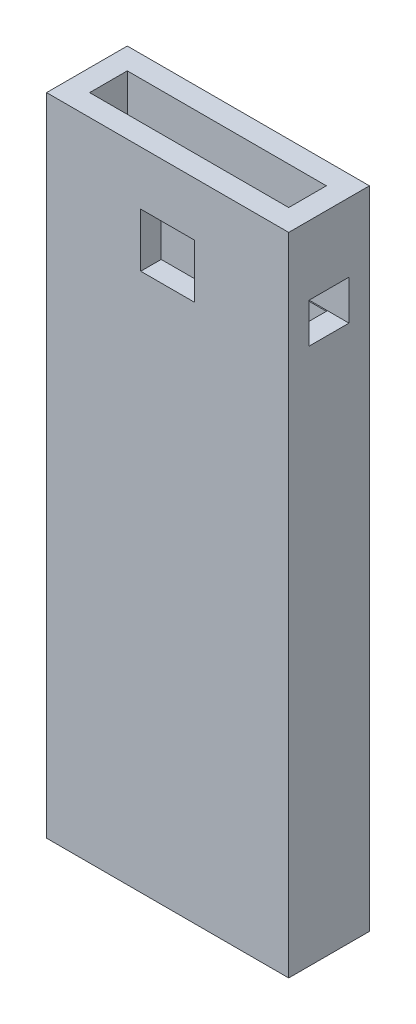
SolidWorks part; units mm, degrees
ref_plane "Front Plane" through (0, 0, 0) normal (0, 0, 1) x (1, 0, 0)
ref_plane "Top Plane" through (0, 0, 0) normal (0, 1, 0) x (1, 0, 0)
ref_plane "Right Plane" through (0, 0, 0) normal (1, 0, 0) x (0, 0, -1)
sketch "Sketch1" plane through (0, 0, 0) normal (0, 1, 0) x (1, 0, 0)
  line L1 (22.5, -7.5) -> (-22.5, -7.5)
  line L2 (22.5, -7.5) -> (22.5, 7.5)
  line L3 (22.5, 7.5) -> (-22.5, 7.5)
  line L4 (-22.5, -7.5) -> (-22.5, 7.5)
  line L5 (22.5, -7.5) -> (-22.5, 7.5) construction
  line L6 (22.5, 7.5) -> (-22.5, -7.5) construction
  point P0 (0, 0)
  dimension "D1" = 45
  dimension "D2" = 15
extrude "Boss-Extrude1" add sketch "Sketch1" along normal mid plane 120
shell "Shell1" thickness 4
sketch "Sketch3" plane through (0, -60, 0) normal (0, -1, 0) x (1, 0, 0)
  line L1 (5, -3.5) -> (-5, -3.5)
  line L2 (5, -3.5) -> (5, 3.5)
  line L3 (5, 3.5) -> (-5, 3.5)
  line L4 (-5, -3.5) -> (-5, 3.5)
  line L5 (5, -3.5) -> (-5, 3.5) construction
  line L6 (5, 3.5) -> (-5, -3.5) construction
  point P0 (0, 0)
  dimension "D1" = 10
  dimension "D2" = 7
extrude "Cut-Extrude2" cut sketch "Sketch3" against normal blind 4
sketch "Sketch4" plane through (0, 0, 7.5) normal (0, 0, 1) x (1, 0, 0)
  line L0 (0, -8.25) -> (0, 8.25) construction
  line L1 (5, 50) -> (-5, 50)
  line L2 (5, 50) -> (5, 40)
  line L3 (5, 40) -> (-5, 40)
  line L4 (-5, 50) -> (-5, 40)
  line L5 (5, 50) -> (-5, 40) construction
  line L6 (5, 40) -> (-5, 50) construction
  line L7 (-22.5, 60) -> (22.5, 60) construction
  point P0 (0, 45)
  dimension "D1" = 10
  dimension "D2" = 10
extrude "Cut-Extrude3" cut sketch "Sketch4" against normal up to next
sketch "Sketch5" plane through (22.5, 0, 0) normal (1, 0, 0) x (0, 0, -1)
  line L0 (0, 24.75) -> (0, -24.75) construction
  line L1 (3.7, 39.8) -> (-3.7, 39.8)
  line L2 (3.7, 39.8) -> (3.7, 47.2)
  line L3 (3.7, 47.2) -> (-3.7, 47.2)
  line L4 (-3.7, 39.8) -> (-3.7, 47.2)
  line L5 (3.7, 39.8) -> (-3.7, 47.2) construction
  line L6 (3.7, 47.2) -> (-3.7, 39.8) construction
  line L7 (-7.5, 60) -> (7.5, 60) construction
  point P0 (0, 43.5)
  dimension "D1" = 20.2
  dimension "D2" = 7.4
  dimension "D3" = 7.4
extrude "Cut-Extrude4" cut sketch "Sketch5" against normal through all
sketch "Sketch6" plane through (0, -60, 0) normal (0, -1, 0) x (1, 0, 0)
  line L0 (24.75, 0) -> (-24.75, 0) construction
  line L1 (-15, 4.2724) -> (-18.7, 2.1362)
  line L2 (-18.7, 2.1362) -> (-18.7, -2.1362)
  line L3 (-18.7, -2.1362) -> (-15, -4.2724)
  line L4 (-15, -4.2724) -> (-11.3, -2.1362)
  line L5 (-11.3, -2.1362) -> (-11.3, 2.1362)
  line L6 (-11.3, 2.1362) -> (-15, 4.2724)
  line L7 (0, -7.5) -> (0, 7.5) construction
  line L8 (22.5, -7.5) -> (-22.5, -7.5) construction
  line L9 (-22.5, 7.5) -> (22.5, 7.5) construction
  line L10 (11.3, 2.1362) -> (15, 4.2724)
  line L11 (11.3, -2.1362) -> (11.3, 2.1362)
  line L12 (15, -4.2724) -> (11.3, -2.1362)
  line L13 (18.7, -2.1362) -> (15, -4.2724)
  line L14 (18.7, 2.1362) -> (18.7, -2.1362)
  line L15 (15, 4.2724) -> (18.7, 2.1362)
  circle A0 centre (-15, 0) radius 3.7 construction
  circle A1 centre (15, 0) radius 3.7 construction
  dimension "D1" = 7.4
  dimension "D2" = 30
extrude "Cut-Extrude5" cut sketch "Sketch6" against normal blind 3.6 from offset 1.2 offset against normal yes
sketch "Sketch7" plane through (0, -60, 0) normal (0, -1, 0) x (1, 0, 0)
  line L0 (24.75, 0) -> (-24.75, 0) construction
  line L1 (0, 7.5) -> (0, -7.5) construction
  line L2 (-22.5, 7.5) -> (22.5, 7.5) construction
  line L3 (22.5, -7.5) -> (-22.5, -7.5) construction
  circle A0 centre (-15, 0) radius 2.1
  circle A1 centre (15, 0) radius 2.1
  dimension "D1" = 4.2
  dimension "D2" = 30
extrude "Cut-Extrude6" cut sketch "Sketch7" against normal up to next
